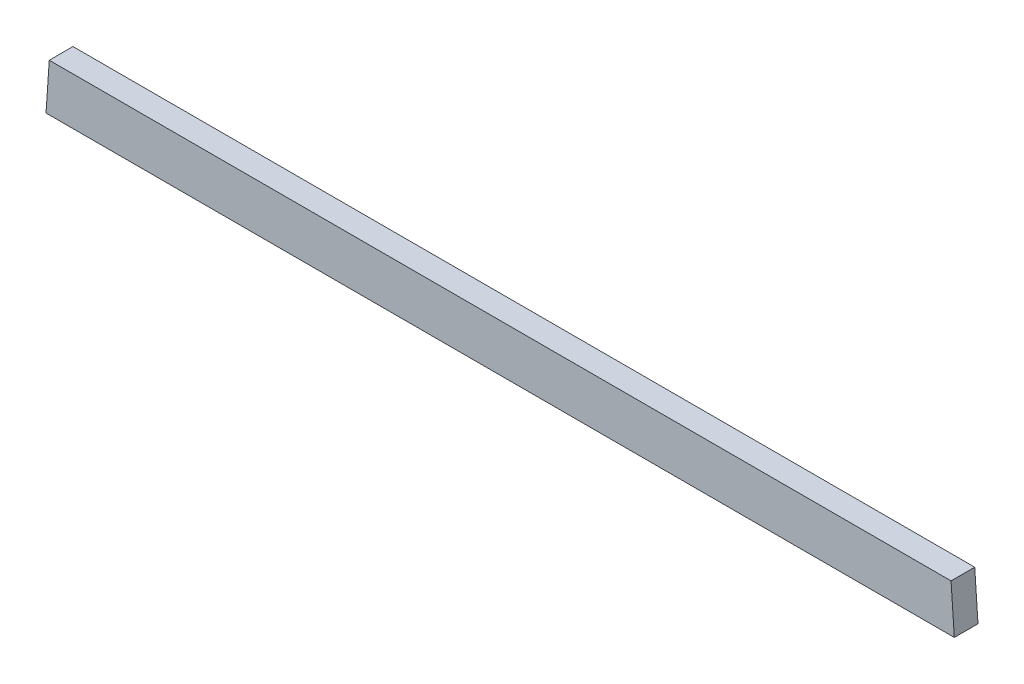
SolidWorks part; units mm, degrees
ref_plane "Front Plane" through (0, 0, 0) normal (0, 0, 1) x (1, 0, 0)
ref_plane "Top Plane" through (0, 0, 0) normal (0, 1, 0) x (1, 0, 0)
ref_plane "Right Plane" through (0, 0, 0) normal (1, 0, 0) x (0, 0, -1)
sketch "Sketch1" plane through (0, 0, 0) normal (0, 0, 1) x (1, 0, 0)
  line L0 (-365.2345, -19.05) -> (365.2345, -19.05)
  line L1 (362.6069, 19.05) -> (365.2345, -19.05)
  line L2 (-362.6069, 19.05) -> (362.6069, 19.05)
  line L3 (-362.6069, 19.05) -> (-365.2345, -19.05)
extrude "Boss-Extrude1" add sketch "Sketch1" along normal blind 19.05
